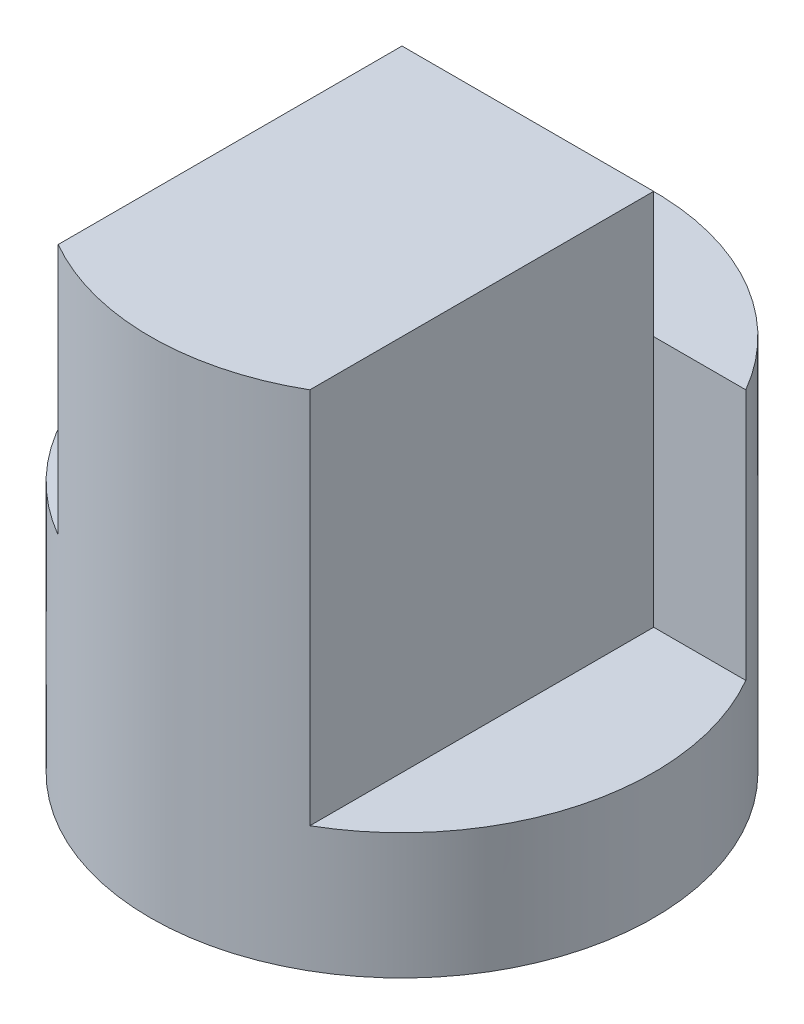
SolidWorks part; units mm, degrees
ref_plane "Front" through (0, 0, 0) normal (0, 0, 1) x (1, 0, 0)
ref_plane "Top" through (0, 0, 0) normal (0, 1, 0) x (1, 0, 0)
ref_plane "Right" through (0, 0, 0) normal (1, 0, 0) x (0, 0, -1)
sketch "Sketch1" plane through (0, 0, 0) normal (0, 1, 0) x (1, 0, 0)
  circle A0 centre (0, 0) radius 2
  dimension "D1" = 4
extrude "Boss-Extrude1" add sketch "Sketch1" along normal blind 4
sketch "Sketch2" plane through (0, 0, 0) normal (0, 0, 1) x (1, 0, 0)
  line L15 (1, 4) -> (1, 1)
  line L16 (2, 4) -> (-2, 4) construction
  line L17 (2, 1) -> (2, 4)
  line L18 (2, 0) -> (2, 4) construction
  line L19 (2, 4) -> (1, 4)
  line L20 (1, 1) -> (2, 1)
  line L22 (-2, 4) -> (-1, 4)
  line L23 (-2, 4) -> (-2, 2)
  line L24 (-2, 2) -> (-1, 2)
  line L25 (-1, 4) -> (-1, 2)
  dimension "D1" = 3
  dimension "D2" = 1
  dimension "D3" = 1
  dimension "D4" = 2
extrude "Cut-Extrude1" cut sketch "Sketch2" against normal blind 1 and the other way blind 3
sketch "Sketch3" plane through (0, 4, 0) normal (0, 1, 0) x (1, 0, 0)
  line L0 (-1.7321, 1) -> (1.7321, 1)
  arc A0 (-1.7321, 1) -> (1.7321, 1) centre (0, 0) cw
  point P5 (0, 0)
  point P6 (0, 0)
extrude "Cut-Extrude2" cut sketch "Sketch3" against normal blind 1
